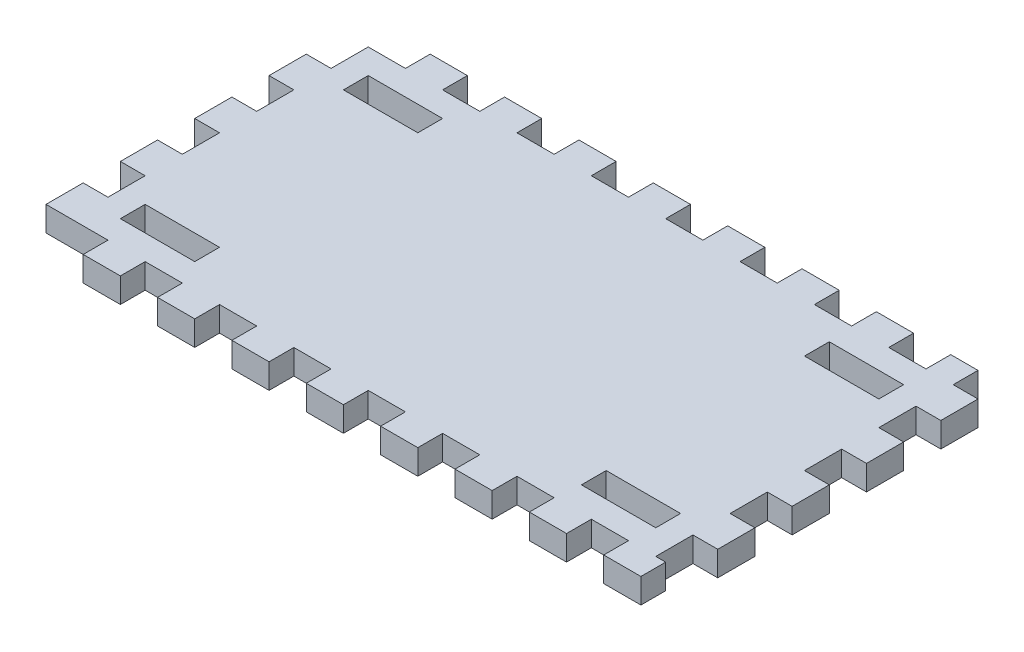
SolidWorks part; units mm, degrees
material "Pine"
ref_plane "Front Plane" through (0, 0, 0) normal (0, 0, 1) x (1, 0, 0)
ref_plane "Top Plane" through (0, 0, 0) normal (0, 1, 0) x (1, 0, 0)
ref_plane "Right Plane" through (0, 0, 0) normal (1, 0, 0) x (0, 0, -1)
sketch "Sketch1" plane through (0, 0, 0) normal (0, 1, 0) x (1, 0, 0)
  line L0 (6.35, -63.5) -> (25.4, -63.5)
  line L1 (0, 0) -> (149.86, 0)
  line L2 (0, 0) -> (0, -76.2)
  line L3 (0, -76.2) -> (149.86, -76.2)
  line L4 (149.86, 0) -> (149.86, -76.2)
  line L5 (6.35, -6.35) -> (25.4, -6.35)
  line L6 (6.35, -6.35) -> (6.35, -12.7)
  line L7 (6.35, -12.7) -> (25.4, -12.7)
  line L8 (25.4, -6.35) -> (25.4, -12.7)
  line L9 (6.35, -63.5) -> (6.35, -69.85)
  line L10 (6.35, -69.85) -> (25.4, -69.85)
  line L11 (25.4, -63.5) -> (25.4, -69.85)
  line L12 (124.46, -63.5) -> (143.51, -63.5)
  line L13 (124.46, -63.5) -> (124.46, -69.85)
  line L14 (124.46, -69.85) -> (143.51, -69.85)
  line L15 (143.51, -63.5) -> (143.51, -69.85)
  line L16 (124.46, -6.35) -> (143.51, -6.35)
  line L17 (124.46, -6.35) -> (124.46, -12.7)
  line L18 (124.46, -12.7) -> (143.51, -12.7)
  line L19 (143.51, -6.35) -> (143.51, -12.7)
  dimension "D1" = 149.86
  dimension "D2" = 76.2
  dimension "D3" = 19.05
  dimension "D4" = 6.35
  dimension "D5" = 6.35
  dimension "D6" = 6.35
  dimension "D7" = 19.05
  dimension "D8" = 6.35
  dimension "D9" = 19.05
  dimension "D10" = 6.35
  dimension "D11" = 19.05
  dimension "D12" = 6.35
  dimension "D13" = 6.35
  dimension "D14" = 6.35
  dimension "D15" = 6.35
  dimension "D16" = 6.35
  dimension "D17" = 6.35
  dimension "D18" = 6.35
extrude "Boss-Extrude1" add sketch "Sketch1" along normal blind 6.35
sketch "Sketch2" plane through (0, 0, 0) normal (0, -1, 0) x (1, 0, 0)
  line L0 (0, 0) -> (0, 76.2) construction
  line L1 (0, 9.525) -> (-6.35, 9.525)
  line L2 (0, 9.525) -> (0, 19.05)
  line L3 (0, 19.05) -> (-6.35, 19.05)
  line L4 (-6.35, 9.525) -> (-6.35, 19.05)
  line L5 (149.86, 0) -> (0, 0) construction
  line L6 (0, 28.575) -> (0, 38.1)
  line L7 (0, 28.575) -> (-6.35, 28.575)
  line L8 (-6.35, 28.575) -> (-6.35, 38.1)
  line L9 (0, 38.1) -> (-6.35, 38.1)
  line L10 (0, 47.625) -> (0, 57.15)
  line L11 (0, 47.625) -> (-6.35, 47.625)
  line L12 (-6.35, 47.625) -> (-6.35, 57.15)
  line L13 (0, 57.15) -> (-6.35, 57.15)
  line L14 (0, 66.675) -> (0, 76.2)
  line L15 (0, 66.675) -> (-6.35, 66.675)
  line L16 (-6.35, 66.675) -> (-6.35, 76.2)
  line L17 (0, 76.2) -> (-6.35, 76.2)
  line L18 (0, 38.1) -> (149.86, 38.1) construction
  line L19 (0, 76.2) -> (149.86, 76.2) construction
  line L20 (149.86, 76.2) -> (149.86, 0) construction
  line L21 (149.86, 66.675) -> (156.21, 66.675)
  line L22 (149.86, 66.675) -> (149.86, 57.15)
  line L23 (149.86, 57.15) -> (156.21, 57.15)
  line L24 (156.21, 66.675) -> (156.21, 57.15)
  line L25 (149.86, 47.625) -> (149.86, 38.1)
  line L26 (149.86, 47.625) -> (156.21, 47.625)
  line L27 (156.21, 47.625) -> (156.21, 38.1)
  line L28 (149.86, 38.1) -> (156.21, 38.1)
  line L29 (149.86, 28.575) -> (149.86, 19.05)
  line L30 (149.86, 28.575) -> (156.21, 28.575)
  line L31 (156.21, 28.575) -> (156.21, 19.05)
  line L32 (149.86, 19.05) -> (156.21, 19.05)
  line L33 (149.86, 9.525) -> (149.86, 0)
  line L34 (149.86, 9.525) -> (156.21, 9.525)
  line L35 (156.21, 9.525) -> (156.21, 0)
  line L36 (149.86, 0) -> (156.21, 0)
  line L37 (28.575, 76.2) -> (28.575, 82.55)
  line L38 (9.525, 76.2) -> (19.05, 76.2)
  line L39 (9.525, 76.2) -> (9.525, 82.55)
  line L40 (9.525, 82.55) -> (19.05, 82.55)
  line L41 (19.05, 76.2) -> (19.05, 82.55)
  line L42 (28.575, 76.2) -> (38.1, 76.2)
  line L43 (38.1, 76.2) -> (38.1, 82.55)
  line L44 (28.575, 82.55) -> (38.1, 82.55)
  line L45 (47.625, 76.2) -> (47.625, 82.55)
  line L46 (47.625, 76.2) -> (57.15, 76.2)
  line L47 (57.15, 76.2) -> (57.15, 82.55)
  line L48 (47.625, 82.55) -> (57.15, 82.55)
  line L49 (66.675, 76.2) -> (66.675, 82.55)
  line L50 (66.675, 76.2) -> (76.2, 76.2)
  line L51 (76.2, 76.2) -> (76.2, 82.55)
  line L52 (66.675, 82.55) -> (76.2, 82.55)
  line L53 (85.725, 76.2) -> (85.725, 82.55)
  line L54 (85.725, 76.2) -> (95.25, 76.2)
  line L55 (95.25, 76.2) -> (95.25, 82.55)
  line L56 (85.725, 82.55) -> (95.25, 82.55)
  line L57 (104.775, 76.2) -> (104.775, 82.55)
  line L58 (104.775, 76.2) -> (114.3, 76.2)
  line L59 (114.3, 76.2) -> (114.3, 82.55)
  line L60 (104.775, 82.55) -> (114.3, 82.55)
  line L61 (123.825, 76.2) -> (123.825, 82.55)
  line L62 (123.825, 76.2) -> (133.35, 76.2)
  line L63 (133.35, 76.2) -> (133.35, 82.55)
  line L64 (123.825, 82.55) -> (133.35, 82.55)
  line L65 (142.875, 76.2) -> (142.875, 82.55)
  line L66 (142.875, 76.2) -> (152.4, 76.2)
  line L67 (152.4, 76.2) -> (152.4, 82.55)
  line L68 (142.875, 82.55) -> (152.4, 82.55)
  line L69 (142.875, 0) -> (149.86, 0)
  line L70 (149.86, 0) -> (149.86, -6.35)
  line L71 (142.875, -6.35) -> (149.86, -6.35)
  line L72 (142.875, 0) -> (142.875, -6.35)
  line L73 (123.825, 0) -> (133.35, 0)
  line L74 (133.35, 0) -> (133.35, -6.35)
  line L75 (123.825, -6.35) -> (133.35, -6.35)
  line L76 (123.825, 0) -> (123.825, -6.35)
  line L77 (104.775, 0) -> (114.3, 0)
  line L78 (114.3, 0) -> (114.3, -6.35)
  line L79 (104.775, -6.35) -> (114.3, -6.35)
  line L80 (104.775, 0) -> (104.775, -6.35)
  line L81 (85.725, 0) -> (95.25, 0)
  line L82 (95.25, 0) -> (95.25, -6.35)
  line L83 (85.725, -6.35) -> (95.25, -6.35)
  line L84 (85.725, 0) -> (85.725, -6.35)
  line L85 (66.675, 0) -> (76.2, 0)
  line L86 (76.2, 0) -> (76.2, -6.35)
  line L87 (66.675, -6.35) -> (76.2, -6.35)
  line L88 (66.675, 0) -> (66.675, -6.35)
  line L89 (47.625, 0) -> (57.15, 0)
  line L90 (57.15, 0) -> (57.15, -6.35)
  line L91 (47.625, -6.35) -> (57.15, -6.35)
  line L92 (47.625, 0) -> (47.625, -6.35)
  line L93 (28.575, 0) -> (38.1, 0)
  line L94 (38.1, 0) -> (38.1, -6.35)
  line L95 (28.575, -6.35) -> (38.1, -6.35)
  line L96 (28.575, 0) -> (28.575, -6.35)
  line L97 (9.525, -6.35) -> (19.05, -6.35)
  line L98 (19.05, 0) -> (19.05, -6.35)
  line L99 (9.525, 0) -> (19.05, 0)
  line L100 (9.525, 0) -> (9.525, -6.35)
  point P21 (0, 0)
  line M63 (0, 76.2) -> (0, 0)
  line M64 (0, 0) -> (149.86, 0)
  line M65 (149.86, 0) -> (149.86, 76.2)
  line M66 (149.86, 76.2) -> (0, 76.2)
  dimension "D1" = 6.35
  dimension "D2" = 9.525
  dimension "D3" = 9.525
  dimension "D5" = 6.35
  dimension "D6" = 9.525
  dimension "D7" = 9.525
  dimension "D8" = 9.525
  dimension "D10" = 6.35
  dimension "D11" = 9.525
  dimension "D12" = 9.525
  dimension "D14" = 9.525
  dimension "D4" = 4
  dimension "D9" = 4
  dimension "D13" = 8
extrude "Boss-Extrude2" add sketch "Sketch2" against normal up to surface (6.35 mm away) contours L13 L12 L11 M63 | L9 L8 L7 M63 | L100 L97 L98 M64 | L92 L91 L90 M64 | L88 L87 L86 M64 | L84 L83 L82 M64 | L76 L75 L74 M64 | L72 L71 L70 M64 | L28 L27 L26 M65 | L68 L65 L66 L67 M66 | L60 L57 L59 M66 | L56 L53 L55 M66 | L44 L37 L43 M66 | L41 L40 L39 M66 | L64 L61 L63 M66 | L16 L17 L14 L15 | L4 L3 L2 L1 | L95 L94 L93 L96 | L79 L78 L77 L80 | L33 L34 L35 L36 | L32 L31 L30 L29 | L23 L24 L21 L22 | L50 L51 L52 L49 | L46 L47 L48 L45 up to face at (74.93, 6.35, 38.1)
